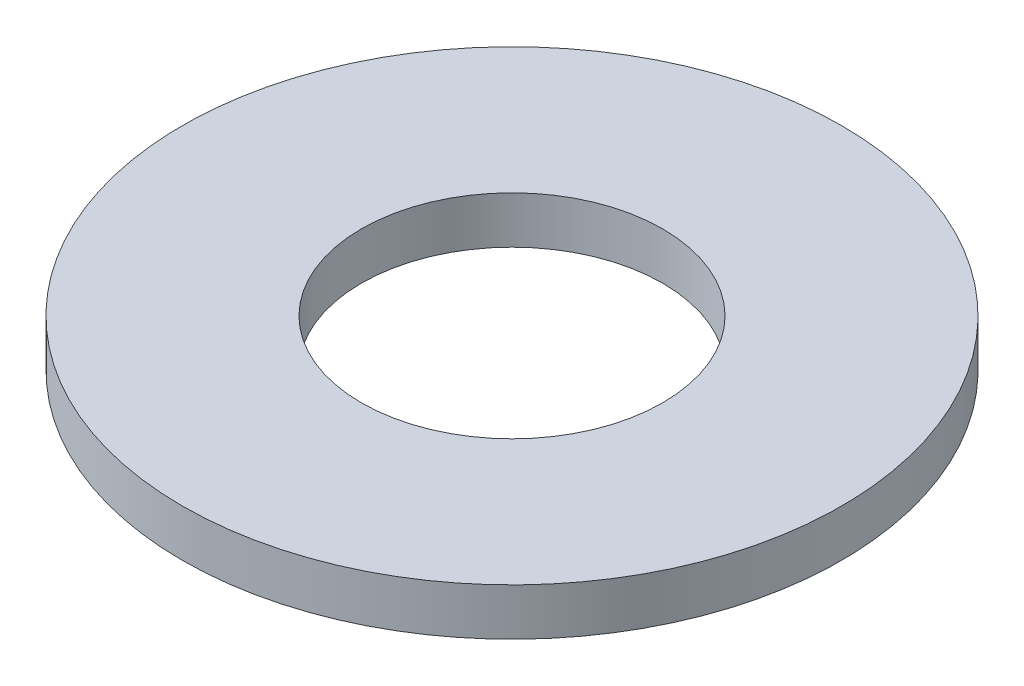
SolidWorks part; units mm, degrees
ref_plane "Alzado" through (0, 0, 0) normal (0, 0, 1) x (1, 0, 0)
ref_plane "Planta" through (0, 0, 0) normal (0, 1, 0) x (1, 0, 0)
ref_plane "Vista lateral" through (0, 0, 0) normal (1, 0, 0) x (0, 0, -1)
sketch "Croquis1" plane through (0, 0, 0) normal (0, 1, 0) x (1, 0, 0)
  circle A0 centre (0, 0) radius 1.6
  circle A1 centre (0, 0) radius 3.5
  dimension "D1" = 7
  dimension "D2" = 3.2
extrude "Saliente-Extruir1" add sketch "Croquis1" along normal blind 0.5
